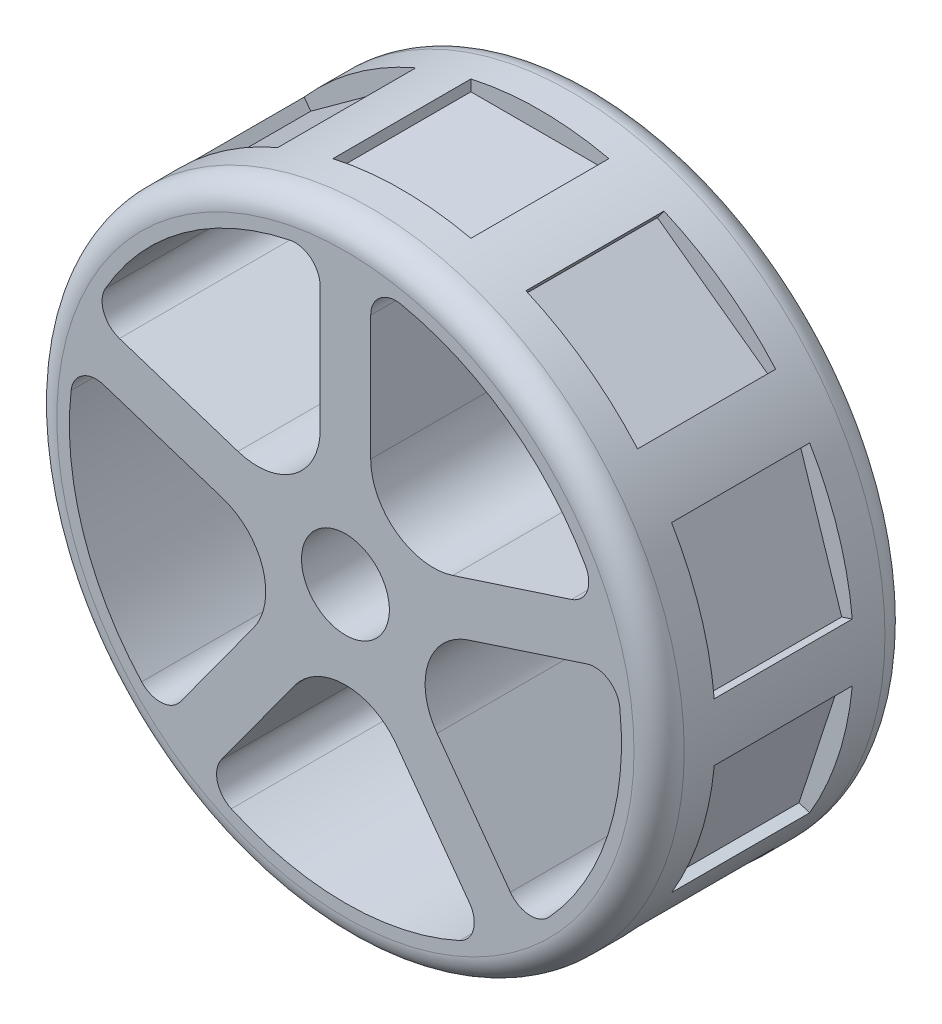
SolidWorks part; units mm, degrees
ref_plane "Front Plane" through (0, 0, 0) normal (0, 0, 1) x (1, 0, 0)
ref_plane "Top Plane" through (0, 0, 0) normal (0, 1, 0) x (1, 0, 0)
ref_plane "Right Plane" through (0, 0, 0) normal (1, 0, 0) x (0, 0, -1)
sketch "Sketch1" plane through (0, 0, 0) normal (0, 0, 1) x (1, 0, 0)
  line L0 (-2.0145, 21.9076) -> (-2.0145, 2.7728)
  line L1 (2.0145, 21.9076) -> (2.0145, 2.7728)
  line L2 (0, 2.1182) -> (0.0846, 2.0907)
  line L3 (20.2128, 8.6858) -> (2.0145, 2.7728)
  line L4 (21.4579, 4.8539) -> (3.2596, -1.0591)
  line L6 (14.5068, -16.5395) -> (3.2596, -1.0591)
  line L7 (11.2471, -18.9077) -> (0, -3.4274)
  line L9 (-11.2471, -18.9077) -> (0, -3.4274)
  line L10 (-14.5068, -16.5395) -> (-3.2596, -1.0591)
  line L12 (-21.4579, 4.8539) -> (-3.2596, -1.0591)
  line L13 (-20.2128, 8.6858) -> (-2.0145, 2.7728)
  circle A0 centre (0, 0) radius 25
  arc A1 (-2.0145, 21.9076) -> (-20.2128, 8.6858) centre (0, 0) ccw
  arc A2 (-21.4579, 4.8539) -> (-14.5068, -16.5395) centre (0, 0) ccw
  arc A3 (-11.2471, -18.9077) -> (11.2471, -18.9077) centre (0, 0) ccw
  arc A4 (14.5068, -16.5395) -> (21.4579, 4.8539) centre (0, 0) ccw
  arc A5 (20.2128, 8.6858) -> (2.0145, 21.9076) centre (0, 0) ccw
  point P26 (0, 0)
  dimension "D1" = 50
  dimension "D2" = 3
  dimension "D4" = 4.0291
  dimension "D3" = 5
extrude "Boss-Extrude1" add sketch "Sketch1" along normal mid plane 20
fillet "Fillet1" radius 2 2 edges at (25, 0, -10) (25, 0, 10)
fillet "Fillet2" radius 2 10 edges at (21.4579, 4.8539, 0) (20.2128, 8.6858, 0) (2.0145, 21.9076, 0) (-2.0145, 21.9076, 0) (-20.2128, 8.6858, 0) (-21.4579, 4.8539, 0) (14.5068, -16.5395, 0) (11.2471, -18.9077, 0) (-11.2471, -18.9077, 0) (-14.5068, -16.5395, 0)
fillet "Fillet3" radius 5 5 edges at (0, -3.4274, 0) (3.2596, -1.0591, 0) (2.0145, 2.7728, 0) (-2.0145, 2.7728, 0) (-3.2596, -1.0591, 0)
sketch "Sketch4" plane through (0, 0, 0) normal (0, 1, 0) x (1, 0, 0)
  line L1 (5.5, -5.5) -> (-5.5, -5.5)
  line L2 (5.5, -5.5) -> (5.5, 5.5)
  line L3 (5.5, 5.5) -> (-5.5, 5.5)
  line L4 (-5.5, -5.5) -> (-5.5, 5.5)
  line L5 (5.5, -5.5) -> (-5.5, 5.5) construction
  line L6 (5.5, 5.5) -> (-5.5, -5.5) construction
  point P0 (0, 0)
  dimension "D1" = 11
extrude "Cut-Extrude2" cut sketch "Sketch4" against normal blind 2.5 from offset 26
pattern_circular "CirPattern1" count 10 over 360 about axis through (0, 0, 0) along (0, 0, 1) of "Cut-Extrude2"
sketch "Sketch2" plane through (0, 0, -10) normal (0, 0, -1) x (-1, 0, 0)
  circle A0 centre (0, 0) radius 3.5
  dimension "D1" = 7
extrude "Cut-Extrude1" cut sketch "Sketch2" against normal through all
